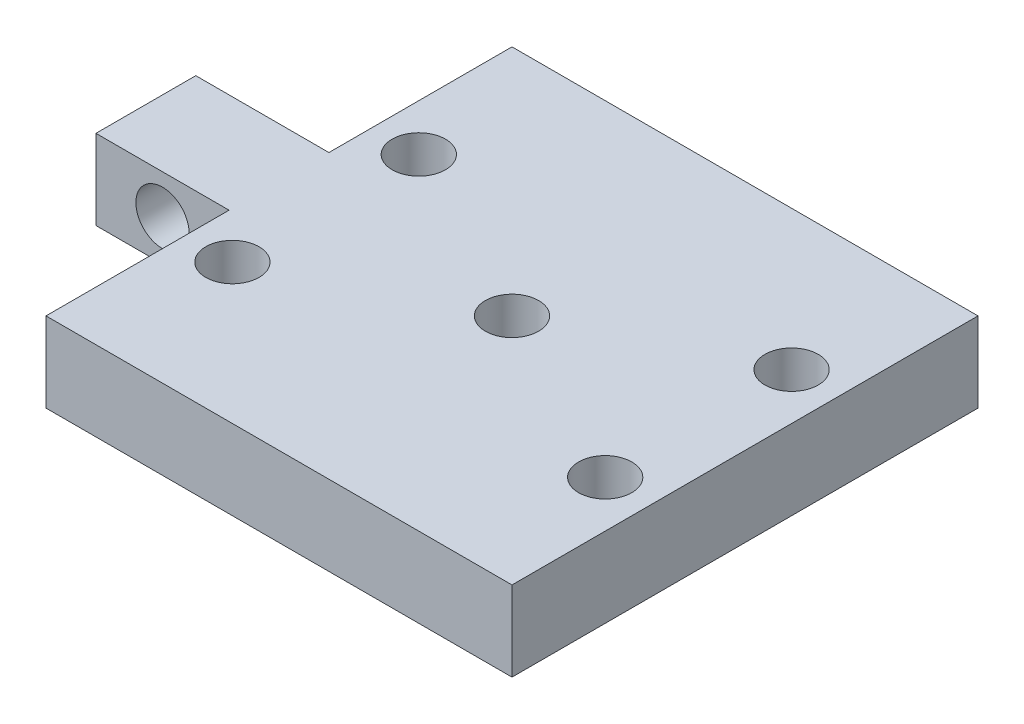
SolidWorks part; units mm, degrees
ref_plane "Alzado" through (0, 0, 0) normal (0, 0, 1) x (1, 0, 0)
ref_plane "Planta" through (0, 0, 0) normal (0, 1, 0) x (1, 0, 0)
ref_plane "Vista lateral" through (0, 0, 0) normal (1, 0, 0) x (0, 0, -1)
sketch "Croquis1" plane through (0, 0, 0) normal (0, 1, 0) x (1, 0, 0)
  line L1 (-35, -35) -> (35, -35)
  line L2 (-35, -35) -> (-35, 35)
  line L3 (-35, 35) -> (35, 35)
  line L4 (35, -35) -> (35, 35)
  line L5 (-35, -35) -> (35, 35) construction
  line L6 (-35, 35) -> (35, -35) construction
  circle A0 centre (0, 0) radius 4
  point P0 (0, 0)
  dimension "D3" = 8
  dimension "D1" = 70
  dimension "D2" = 70
extrude "Saliente-Extruir1" add sketch "Croquis1" along normal blind 12
sketch "Croquis3" plane through (0, 12, 0) normal (0, 1, 0) x (1, 0, 0)
  circle A0 centre (-28, 14) radius 4
  circle A1 centre (28, 14) radius 4
  circle A2 centre (28, -14) radius 4
  circle A3 centre (-28, -14) radius 4
  dimension "D1" = 8
  dimension "D2" = 28
  dimension "D3" = 14
  dimension "D4" = 28
  dimension "D5" = 14
extrude "Cortar-Extruir2" cut sketch "Croquis3" against normal blind 15
sketch "Croquis4" plane through (0, 12, 0) normal (0, 1, 0) x (1, 0, 0)
  line L4 (-15, 7.5) -> (-15, -7.5)
  line L6 (-15, 7.5) -> (-55, 7.5)
  line L7 (-55, 7.5) -> (-55, -7.5)
  line L8 (-55, -7.5) -> (-15, -7.5)
  point P2 (-15, 0)
  dimension "D1" = 15
  dimension "D2" = 40
  dimension "D3" = 15
extrude "Saliente-Extruir2" add sketch "Croquis4" against normal blind 12
sketch "Croquis6" plane through (0, 0, 7.5) normal (0, 0, 1) x (1, 0, 0)
  line L0 (-55, 0) -> (-55, 12) construction
  line L2 (-55, 12) -> (-35, 12) construction
  circle A0 centre (-45, 6) radius 4
  dimension "D1" = 8
  dimension "D2" = 10
  dimension "D3" = 6
extrude "Cortar-Extruir4" cut sketch "Croquis6" against normal up to surface (15 mm away) up to face at (-45, 6, -7.5)
